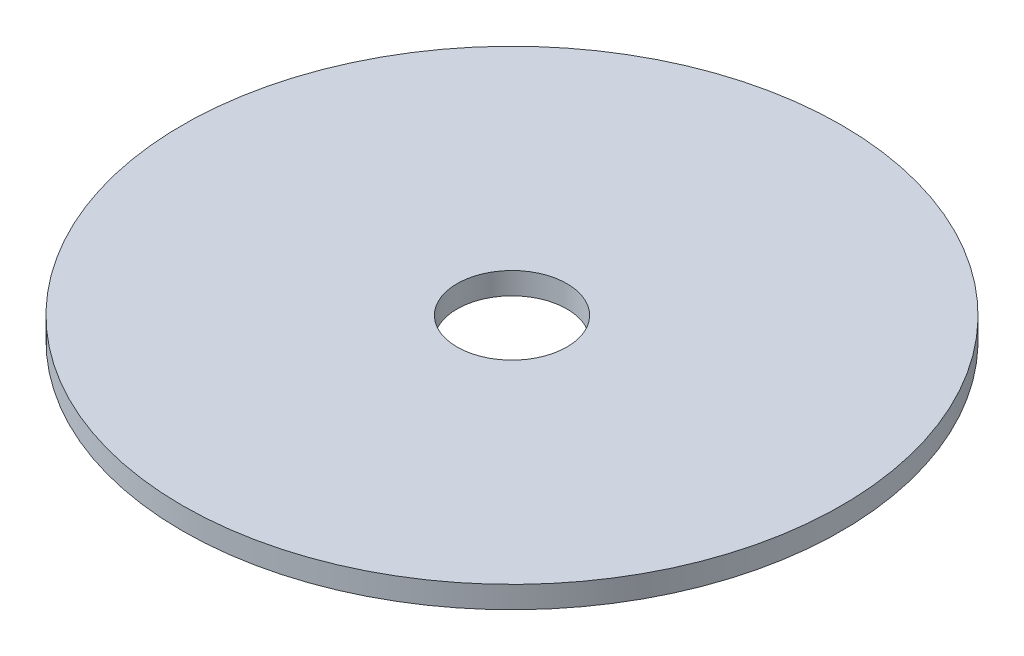
SolidWorks part; units mm, degrees
ref_plane "Front Plane" through (0, 0, 0) normal (0, 0, 1) x (1, 0, 0)
ref_plane "Top Plane" through (0, 0, 0) normal (0, 1, 0) x (1, 0, 0)
ref_plane "Right Plane" through (0, 0, 0) normal (1, 0, 0) x (0, 0, -1)
sketch "Sketch1" plane through (0, 0, 0) normal (0, 1, 0) x (1, 0, 0)
  circle A0 centre (0, 0) radius 60
  dimension "D1" = 120
extrude "Boss-Extrude1" add sketch "Sketch1" along normal blind 4
sketch "Sketch2" plane through (0, 4, 0) normal (0, 1, 0) x (1, 0, 0)
  circle A0 centre (0, 0) radius 10
  dimension "D1" = 20
extrude "Cut-Extrude1" cut sketch "Sketch2" against normal blind 10
sketch "Croquis1" plane through (0, 4, 0) normal (0, 1, 0) x (1, 0, 0)
  line L0 (0, 0) -> (0, 60) construction
  circle A0 centre (0, 0) radius 60 construction
